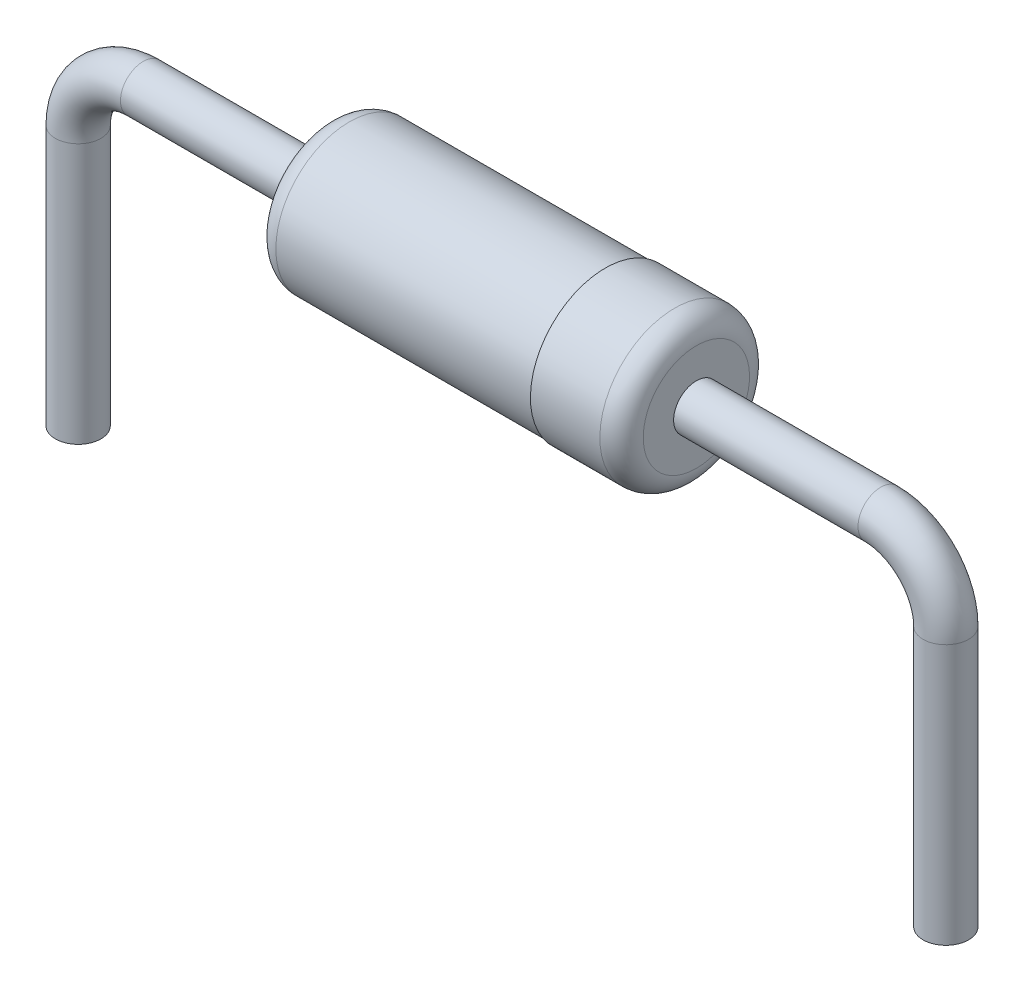
SolidWorks part; units mm, degrees
ref_plane "x/y" through (0, 0, 0) normal (0, 0, 1) x (1, 0, 0)
ref_plane "x/z" through (0, 0, 0) normal (0, 1, 0) x (1, 0, 0)
ref_plane "y/z" through (0, 0, 0) normal (1, 0, 0) x (0, 0, -1)
sketch "Sketch2" plane through (0, 0, 0) normal (0, 0, 1) x (1, 0, 0)
  line L0 (0, -2.54) -> (0, 0.508)
  line L1 (0.762, 1.27) -> (2.921, 1.27)
  arc A0 (0.762, 1.27) -> (0, 0.508) centre (0.762, 0.508) ccw
  dimension "D4" = 0.762
  dimension "D1" = 3.048
  dimension "D2" = 2.54
  dimension "D3" = 2.921
ref_plane "Plane1" through (0, -2.54, 0) normal (0, 1, 0) x (-1, 0, 0)
sketch "Sketch3" plane through (0, -2.54, 0) normal (0, 1, 0) x (-1, 0, 0)
  circle A0 centre (0, 0) radius 0.2665
  dimension "D1" = 0.533
sweep "Base-Sweep" add profiles "Sketch3" path "Sketch2"
sketch "Sketch4" plane through (2.921, 0, 0) normal (1, 0, 0) x (0, 0, -1)
  circle A0 centre (0, 1.27) radius 0.86
  circle A1 centre (0, 1.27) radius 0.2665 construction
  dimension "D1" = 1.72
extrude "Boss-Extrude1" add sketch "Sketch4" along normal blind 2.159
mirror "Boss-Mirror1" about plane through (5.08, 1.27, 0) normal (1, 0, 0) of bodies 102
ref_plane "Plane2" through (6.731, 0, 0) normal (-1, 0, 0) x (0, 0, 1)
sketch "Sketch5" plane through (7.239, 0, 0) normal (-1, 0, 0) x (0, 0, 1)
  circle A0 centre (0, 1.27) radius 0.8763
  dimension "D1" = 1.7526
extrude "Boss-Extrude2" add sketch "Sketch5" along normal blind 1.0668
fillet "Fillet2" radius 0.254 2 edges at (2.921, 2.13, 0) (7.239, 0.3937, 0)
